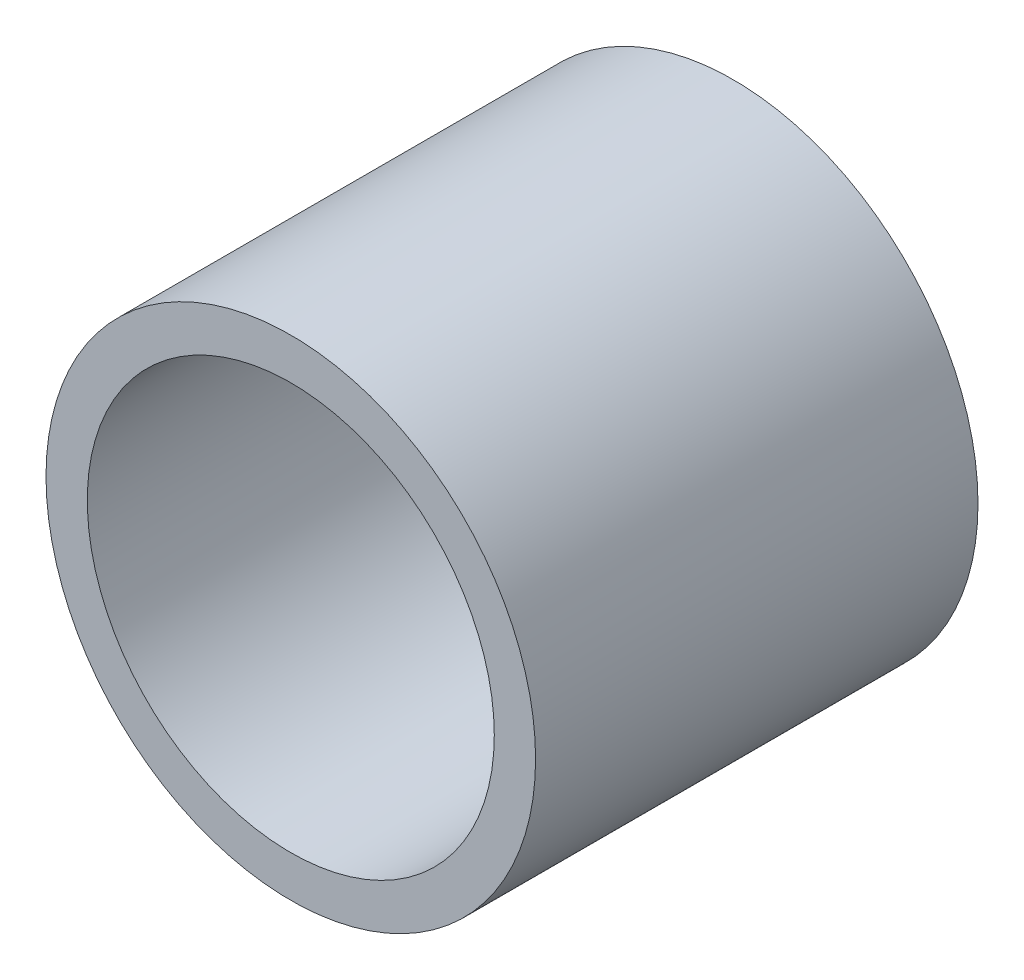
SolidWorks part; units mm, degrees
ref_plane "Front Plane" through (0, 0, 0) normal (0, 0, 1) x (1, 0, 0)
ref_plane "Top Plane" through (0, 0, 0) normal (0, 1, 0) x (1, 0, 0)
ref_plane "Right Plane" through (0, 0, 0) normal (1, 0, 0) x (0, 0, -1)
sketch "Sketch1" plane through (0, 0, 0) normal (0, 0, 1) x (1, 0, 0)
  circle A0 centre (0, 0) radius 21.082
  dimension "Pipe OD" = 42.164
extrude "Extrude-Thin1" add sketch "Sketch1" along normal mid plane 38.1 thin thin type one direction reverse wall 3.556
